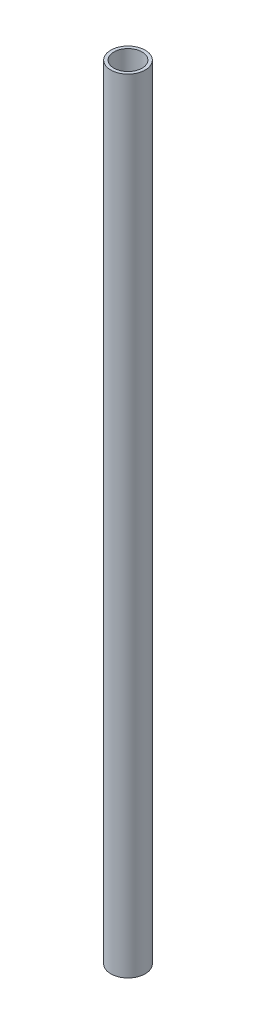
SolidWorks part; units mm, degrees
ref_plane "前视基准面" through (0, 0, 0) normal (0, 0, 1) x (1, 0, 0)
ref_plane "上视基准面" through (0, 0, 0) normal (0, 1, 0) x (1, 0, 0)
ref_plane "右视基准面" through (0, 0, 0) normal (1, 0, 0) x (0, 0, -1)
sketch "草图1" plane through (0, 0, 0) normal (0, 1, 0) x (1, 0, 0)
  circle A0 centre (0, 0) radius 11
  dimension "D1" = 22
extrude "凸台-拉伸1" add sketch "草图1" along normal blind 20
sketch "草图2" plane through (0, 20, 0) normal (0, 1, 0) x (1, 0, 0)
  circle A0 centre (0, 0) radius 11
  dimension "D1" = 22
extrude "凸台-拉伸2" add sketch "草图2" along normal blind 480
sketch "草图4" plane through (0, 0, 0) normal (0, -1, 0) x (1, 0, 0)
  circle A0 centre (0, 0) radius 9
  dimension "D1" = 18
extrude "切除-拉伸1" cut sketch "草图4" against normal through all
